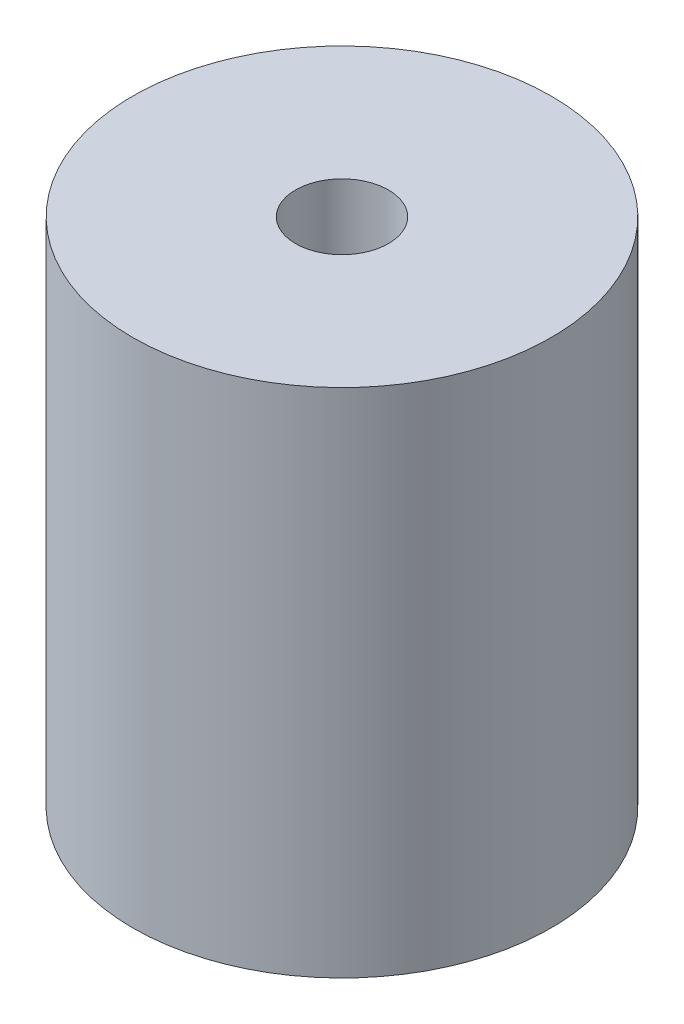
SolidWorks part; units mm, degrees
ref_plane "Front Plane" through (0, 0, 0) normal (0, 0, 1) x (1, 0, 0)
ref_plane "Top Plane" through (0, 0, 0) normal (0, 1, 0) x (1, 0, 0)
ref_plane "Right Plane" through (0, 0, 0) normal (1, 0, 0) x (0, 0, -1)
sketch "Sketch1" plane through (0, 0, 0) normal (0, 1, 0) x (1, 0, 0)
  circle A0 centre (0, 0) radius 22.5
  dimension "D1" = 45
extrude "Boss-Extrude1" add sketch "Sketch1" along normal blind 55
sketch "Sketch2" plane through (0, 55, 0) normal (0, 1, 0) x (1, 0, 0)
  circle A0 centre (0, 0) radius 5
  dimension "D1" = 10
extrude "Cut-Extrude1" cut sketch "Sketch2" against normal blind 10
sketch "Sketch3" plane through (0, 0, 0) normal (0, -1, 0) x (1, 0, 0)
  circle A0 centre (0, 0) radius 5
  dimension "D1" = 10
extrude "Cut-Extrude2" cut sketch "Sketch3" against normal blind 10
